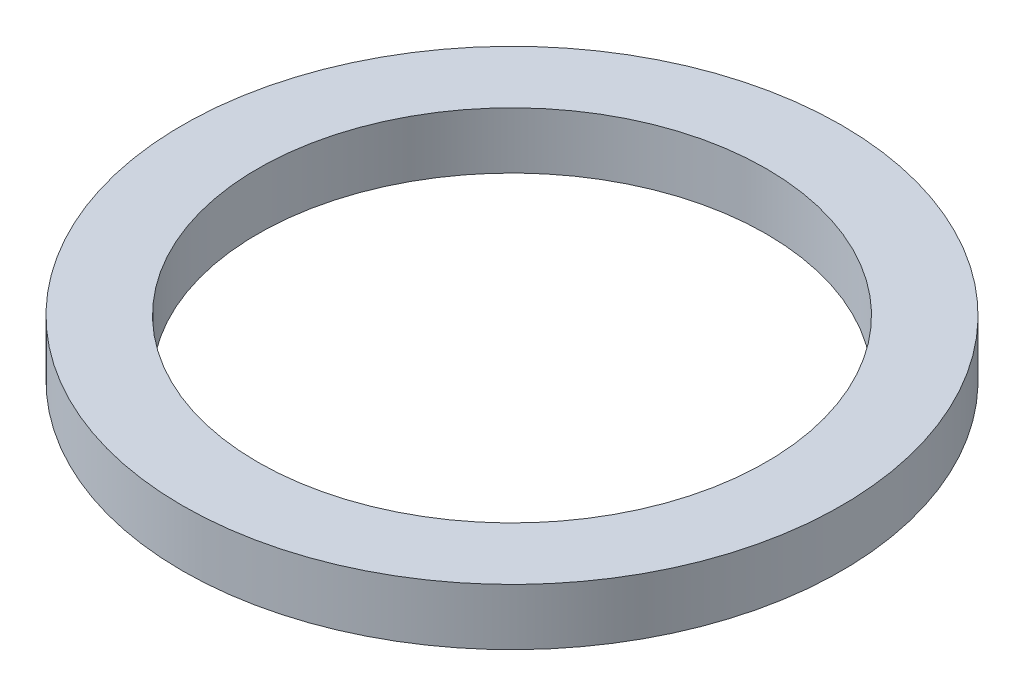
SolidWorks part; units mm, degrees
material "NBR"
ref_plane "Front Plane" through (0, 0, 0) normal (0, 0, 1) x (1, 0, 0)
ref_plane "Top Plane" through (0, 0, 0) normal (0, 1, 0) x (1, 0, 0)
ref_plane "Right Plane" through (0, 0, 0) normal (1, 0, 0) x (0, 0, -1)
sketch "Sketch1" plane through (0, 0, 0) normal (0, 1, 0) x (1, 0, 0)
  circle A0 centre (0, 0) radius 3.429
  circle A1 centre (0, 0) radius 4.445
  dimension "D2" = 8.89
  dimension "D1" = 1.016
extrude "Boss-Extrude1" add sketch "Sketch1" along normal blind 0.762
equation "\"w\"= 0.04"
equation "\"D1@Sketch1\"=\"w\""
equation "\"D2@Sketch1\"= .37 - .02 '20 thou smaller than channel diam"
